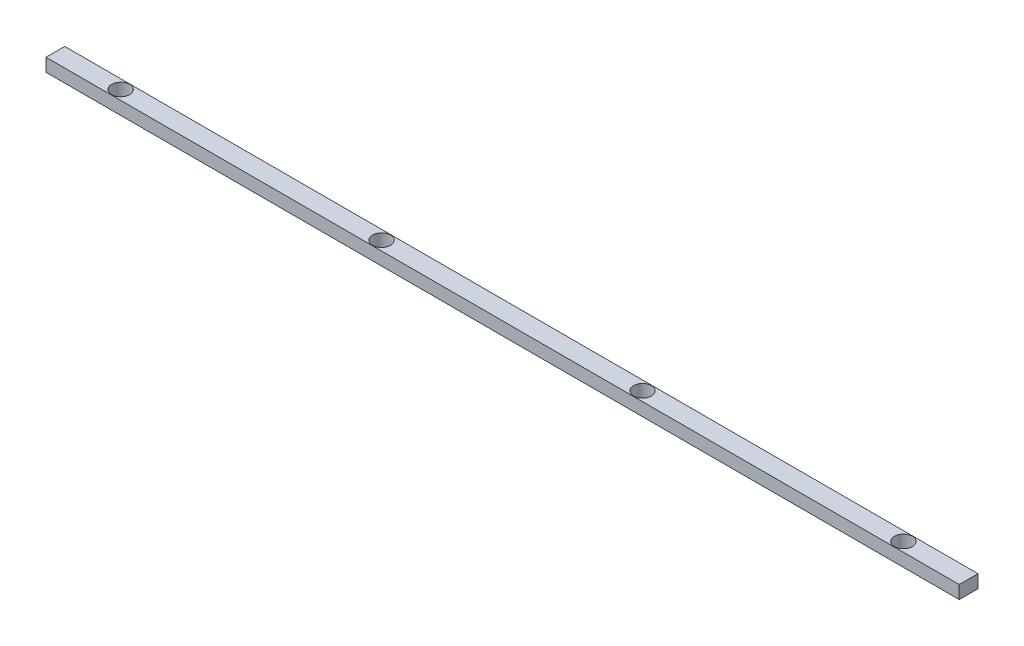
SolidWorks part; units mm, degrees
material "PVC Rigid"
ref_plane "Front Plane" through (0, 0, 0) normal (0, 0, 1) x (1, 0, 0)
ref_plane "Top Plane" through (0, 0, 0) normal (0, 1, 0) x (1, 0, 0)
ref_plane "Right Plane" through (0, 0, 0) normal (1, 0, 0) x (0, 0, -1)
sketch "Sketch1" plane through (0, 0, 0) normal (0, 1, 0) x (1, 0, 0)
  line L1 (-177.8, -3.6512) -> (177.8, -3.6512)
  line L2 (-177.8, -3.6512) -> (-177.8, 3.6513)
  line L3 (-177.8, 3.6513) -> (177.8, 3.6513)
  line L4 (177.8, -3.6512) -> (177.8, 3.6513)
  line L5 (-177.8, -3.6512) -> (177.8, 3.6513) construction
  line L6 (-177.8, 3.6513) -> (177.8, -3.6512) construction
  point P0 (0, 0)
  dimension "D1" = 7.3025
  dimension "D2" = 355.6
extrude "Boss-Extrude1" add sketch "Sketch1" along normal blind 5.08
sketch "Sketch2" plane through (0, 5.08, 0) normal (0, 1, 0) x (1, 0, 0)
  line L0 (-152.4, 0) -> (-50.8, 0) construction
  line L1 (-177.8, 3.6513) -> (-177.8, -3.6512) construction
  line L2 (177.8, -3.6512) -> (177.8, 3.6513) construction
  line L4 (-177.8, 0) -> (177.8, 0) construction
  circle A0 centre (-152.4, 0) radius 3.4925
  circle A1 centre (-50.8, 0) radius 3.4925
  circle A2 centre (50.8, 0) radius 3.4925
  circle A3 centre (152.4, 0) radius 3.4925
  dimension "D2" = 25.4
  dimension "D1" = 6.985
  dimension "D3" = 101.6
extrude "Cut-Extrude1" cut sketch "Sketch2" against normal through all
